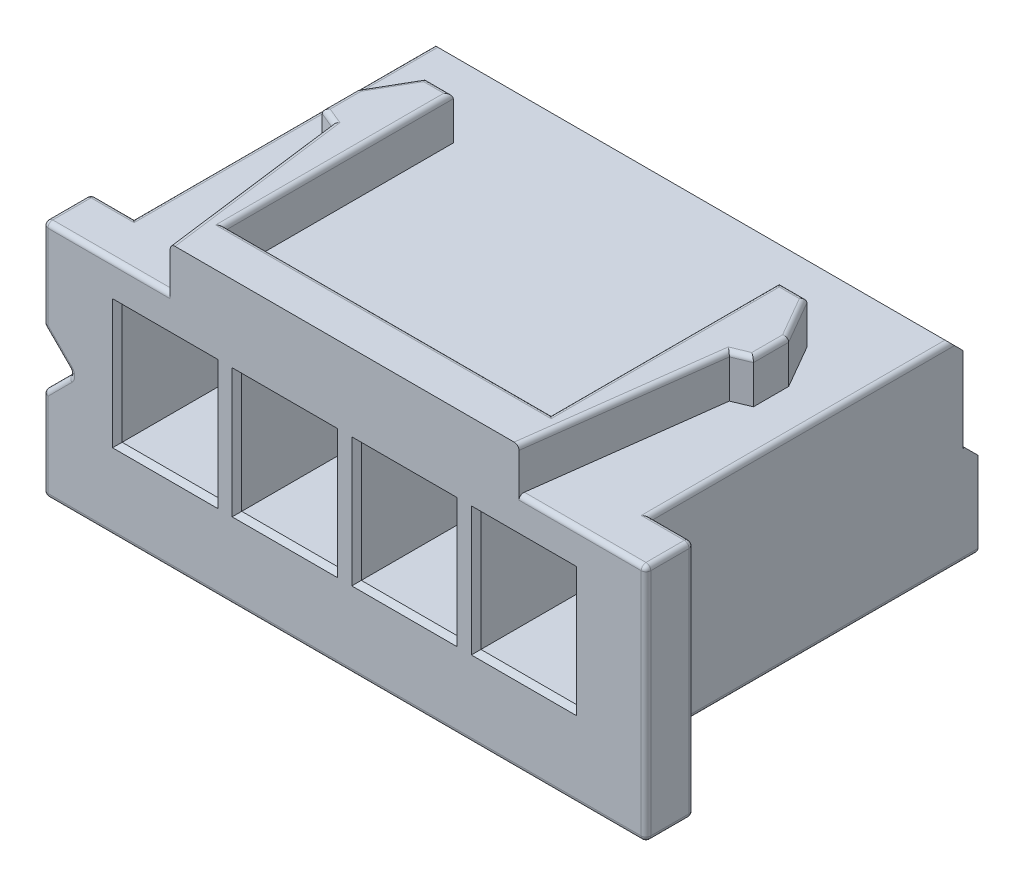
SolidWorks part; units mm, degrees
ref_plane "Front Plane" through (0, 0, 0) normal (0, 0, 1) x (1, 0, 0)
ref_plane "Top Plane" through (0, 0, 0) normal (0, 1, 0) x (1, 0, 0)
ref_plane "Right Plane" through (0, 0, 0) normal (1, 0, 0) x (0, 0, -1)
sketch "Sketch2" plane through (0, 0, 0) normal (1, 0, 0) x (0, 0, -1)
  line L0 (0, 4.1167) -> (6.25, 4.1167)
  line L1 (0, 4.1167) -> (0, 0)
  line L2 (0, 0) -> (6.84, 0)
  line L3 (6.84, 1.7867) -> (6.84, 0)
  line L4 (6.53, 3.8367) -> (6.53, 2.0667)
  line L5 (6.53, 2.0667) -> (6.56, 2.0667)
  line L6 (6.56, 2.0667) -> (6.84, 1.7867)
  line L7 (6.25, 4.1167) -> (6.53, 3.8367)
extrude "Boss-Extrude1" add sketch "Sketch2" along normal blind 10.8
sketch "Sketch3" plane through (0, 0, 0) normal (0, 0, 1) x (1, 0, 0)
  line L0 (-0.9, 1.0167) -> (-0.9, -0.8833)
  line L9 (-1.3111, 1.6167) -> (0.7111, 1.6167) construction
  line L10 (5.4, -0.5092) -> (5.4, 4.6303) construction
  line L11 (-0.9, 4.1167) -> (-0.9, 2.2167)
  line L12 (11.7, 4.1167) -> (11.7, -0.8833)
  line L13 (-0.9, 4.1167) -> (11.7, 4.1167)
  line L14 (-0.9, -0.8833) -> (11.7, -0.8833)
  line L16 (-0.9, 2.2167) -> (-0.3, 1.6167)
  line L17 (-0.3, 1.6167) -> (-0.9, 1.0167)
  point P6 (-0.3, 1.6167)
extrude "Boss-Extrude2" add sketch "Sketch3" along normal blind 1
sketch "Sketch4" plane through (0, 4.1167, 0) normal (0, 1, 0) x (1, 0, 0)
  line L0 (1.2493, 2.8914) -> (0.8938, 3.0394)
  line L1 (9.9062, 3.7763) -> (9.9062, 3.0394)
  line L2 (0.8938, 3.7763) -> (1.4147, 4.6785)
  line L3 (1.993, -0.09) -> (8.807, -0.09)
  line L4 (1.7549, -1) -> (9.0451, -1)
  line L5 (9.3853, 4.6785) -> (9.9062, 3.7763)
  line L6 (0.8938, 3.0394) -> (0.8938, 3.7763)
  line L7 (9.5507, 2.8914) -> (9.0451, -1)
  line L8 (1.993, 4.6785) -> (1.993, -0.09)
  line L9 (8.807, 4.6785) -> (9.3853, 4.6785)
  line L10 (1.2493, 2.8914) -> (1.7549, -1)
  line L11 (9.9062, 3.0394) -> (9.5507, 2.8914)
  line L12 (1.4147, 4.6785) -> (1.993, 4.6785)
  line L13 (8.807, -0.09) -> (8.807, 4.6785)
  line L16 (5.4, -2.0966) -> (5.4, 4.1239) construction
extrude "Boss-Extrude3" add sketch "Sketch4" along normal blind 0.9
sketch "Sketch5" plane through (0, 0, 1) normal (0, 0, 1) x (1, 0, 0)
  line L0 (-0.9, 4.1167) -> (-0.9, 2.2167) construction
  line L1 (0.65, 3.3167) -> (2.65, 3.3167)
  line L2 (0.65, 3.3167) -> (0.65, 0.8167)
  line L3 (0.65, 0.8167) -> (2.65, 0.8167)
  line L4 (2.65, 3.3167) -> (2.65, 0.8167)
  line L5 (1.7549, 4.1167) -> (-0.9, 4.1167) construction
  line L6 (3.15, 3.3167) -> (5.15, 3.3167)
  line L7 (3.15, 3.3167) -> (3.15, 0.8167)
  line L8 (3.15, 0.8167) -> (5.15, 0.8167)
  line L9 (5.15, 3.3167) -> (5.15, 0.8167)
  line L10 (5.65, 3.3167) -> (7.65, 3.3167)
  line L11 (5.65, 3.3167) -> (5.65, 0.8167)
  line L12 (5.65, 0.8167) -> (7.65, 0.8167)
  line L13 (7.65, 3.3167) -> (7.65, 0.8167)
  line L14 (8.15, 3.3167) -> (10.15, 3.3167)
  line L15 (8.15, 3.3167) -> (8.15, 0.8167)
  line L16 (8.15, 0.8167) -> (10.15, 0.8167)
  line L17 (10.15, 3.3167) -> (10.15, 0.8167)
  dimension "D1" = 2
  dimension "D2" = 2.5
  dimension "D3" = 1.55
  dimension "D4" = 0.8
  dimension "D5" = 4
extrude "Cut-Extrude1" cut sketch "Sketch5" against normal blind 5.2
sketch "Sketch6" plane through (0, 0, -6.84) normal (0, 0, -1) x (-1, 0, 0)
  line L0 (-9.55, 0.8) -> (-8.75, 0.8)
  line L1 (-8.75, 0.8) -> (-8.55, 0)
  line L2 (-10.8, 0) -> (0, 0) construction
  line L3 (-9.55, 0.8) -> (-9.75, 0)
  line L4 (-10.8, 0) -> (0, 0) construction
  line L5 (-9.75, 0) -> (-8.55, 0)
  line L6 (-10.8, 0) -> (-10.8, 1.7867) construction
  line L7 (-7.05, 0.8) -> (-6.25, 0.8)
  line L8 (-6.25, 0.8) -> (-6.05, 0)
  line L9 (-7.05, 0.8) -> (-7.25, 0)
  line L10 (-7.25, 0) -> (-6.05, 0)
  line L11 (-4.55, 0.8) -> (-3.75, 0.8)
  line L12 (-3.75, 0.8) -> (-3.55, 0)
  line L13 (-4.55, 0.8) -> (-4.75, 0)
  line L14 (-4.75, 0) -> (-3.55, 0)
  line L15 (-2.05, 0.8) -> (-1.25, 0.8)
  line L16 (-1.25, 0.8) -> (-1.05, 0)
  line L17 (-2.05, 0.8) -> (-2.25, 0)
  line L18 (-2.25, 0) -> (-1.05, 0)
  dimension "D1" = 0.8
  dimension "D2" = 0.8
  dimension "D3" = 0.2
  dimension "D4" = 1.25
  dimension "D5" = 1.2
  dimension "D6" = 4
extrude "Cut-Extrude2" cut sketch "Sketch6" against normal blind 3.75
sketch "Sketch7" plane through (0, 0, -6.53) normal (0, 0, -1) x (-1, 0, 0)
  line L0 (-10.8, 3.8367) -> (0, 3.8367) construction
  line L1 (-9.65, 3.3367) -> (-8.65, 3.3367)
  line L2 (-9.65, 3.3367) -> (-9.65, 2.3367)
  line L3 (-9.65, 2.3367) -> (-8.65, 2.3367)
  line L4 (-8.65, 3.3367) -> (-8.65, 2.3367)
  line L5 (-10.8, 4.1167) -> (-10.8, 0) construction
  line L6 (-7.15, 3.3367) -> (-6.15, 3.3367)
  line L7 (-7.15, 3.3367) -> (-7.15, 2.3367)
  line L8 (-7.15, 2.3367) -> (-6.15, 2.3367)
  line L9 (-6.15, 3.3367) -> (-6.15, 2.3367)
  line L10 (-4.65, 3.3367) -> (-3.65, 3.3367)
  line L11 (-4.65, 3.3367) -> (-4.65, 2.3367)
  line L12 (-4.65, 2.3367) -> (-3.65, 2.3367)
  line L13 (-3.65, 3.3367) -> (-3.65, 2.3367)
  line L14 (-2.15, 3.3367) -> (-1.15, 3.3367)
  line L15 (-2.15, 3.3367) -> (-2.15, 2.3367)
  line L16 (-2.15, 2.3367) -> (-1.15, 2.3367)
  line L17 (-1.15, 3.3367) -> (-1.15, 2.3367)
  dimension "D1" = 1
  dimension "D2" = 1
  dimension "D3" = 0.5
  dimension "D4" = 1.15
  dimension "D5" = 4
extrude "Cut-Extrude3" cut sketch "Sketch7" against normal blind 2.5
fillet "Fillet1" radius 0.1 45 edges at (9.2979, 5.0167, -0.9457) (9.7285, 5.0167, -2.9654) (9.9062, 5.0167, -3.4078) (9.6458, 5.0167, -4.2274) (9.0962, 5.0167, -4.6785) (8.807, 5.0167, -2.2942) (5.4, 5.0167, 0.09) (1.993, 5.0167, -2.2942) (1.7038, 5.0167, -4.6785) (1.1542, 5.0167, -4.2274) (0.8938, 5.0167, -3.4078) (1.0715, 5.0167, -2.9654) (1.5021, 5.0167, -0.9457) (-0.6, 1.9167, 0) (-0.6, 1.3167, 1) (0, 0, -3.42) (10.8, 0, -3.42) (-0.9, 3.1667, 0) (-0.6, 1.3167, 0) (-0.9, 0.0667, 0) (5.4, -0.8833, 0) (11.7, 1.6167, 0) (-0.9, 0.0667, 1) (-0.6, 1.9167, 1) (-0.9, 3.1667, 1) (5.4, -0.8833, 1) (11.7, 1.6167, 1) (-0.3, 1.6167, 0.5) (-0.9, 1.0167, 0.5) (-0.9, 2.2167, 0.5) (-0.9, 4.1167, 0.5) (-0.9, -0.8833, 0.5) (11.7, -0.8833, 0.5) (11.7, 4.1167, 0.5) (0.525, 0, -6.84) (2.9, 0, -6.84) (5.4, 0, -6.84) (7.9, 0, -6.84) (10.275, 0, -6.84)
chamfer "Chamfer1" distance 0.1 angle 45 32 edges at (1.65, 2.3367, -6.53) (1.15, 2.8367, -6.53) (1.65, 3.3367, -6.53) (2.15, 2.8367, -6.53) (4.15, 2.3367, -6.53) (3.65, 2.8367, -6.53) (4.15, 3.3367, -6.53) (4.65, 2.8367, -6.53) (6.65, 2.3367, -6.53) (6.15, 2.8367, -6.53) (6.65, 3.3367, -6.53) (7.15, 2.8367, -6.53) (9.15, 2.3367, -6.53) (8.65, 2.8367, -6.53) (9.15, 3.3367, -6.53) (9.65, 2.8367, -6.53) (9.15, 0.8167, 1) (10.15, 2.0667, 1) (9.15, 3.3167, 1) (8.15, 2.0667, 1) (6.65, 0.8167, 1) (7.65, 2.0667, 1) (6.65, 3.3167, 1) (5.65, 2.0667, 1) (4.15, 0.8167, 1) (5.15, 2.0667, 1) (4.15, 3.3167, 1) (3.15, 2.0667, 1) (1.65, 0.8167, 1) (2.65, 2.0667, 1) (1.65, 3.3167, 1) (0.65, 2.0667, 1)
